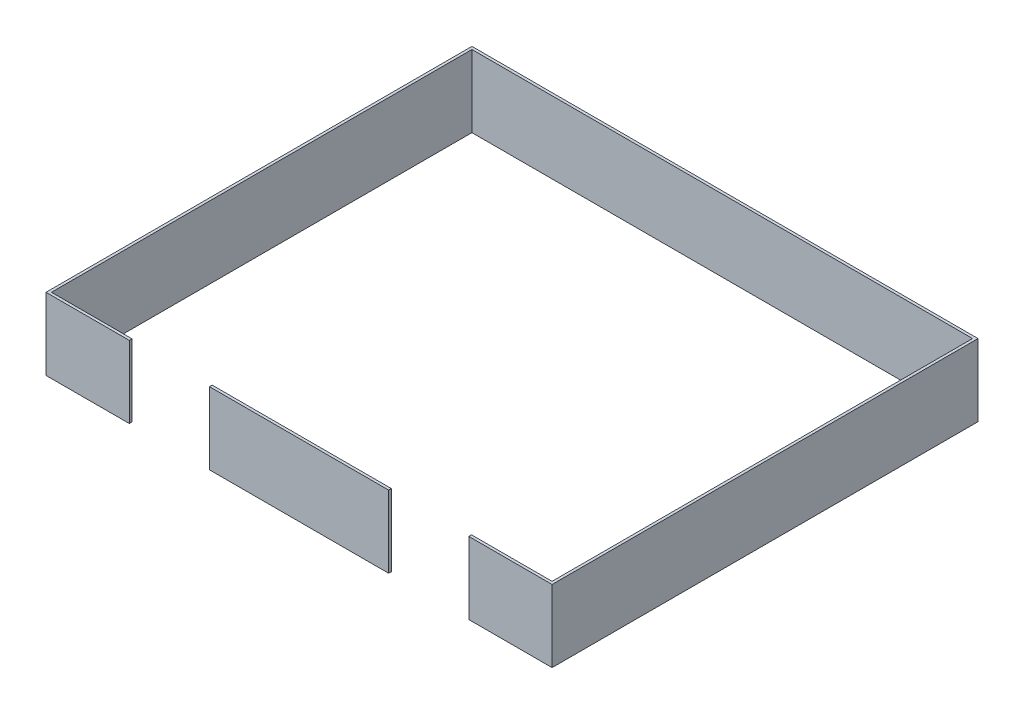
SolidWorks part; units mm, degrees
ref_plane "Front Plane" through (0, 0, 0) normal (0, 0, 1) x (1, 0, 0)
ref_plane "Top Plane" through (0, 0, 0) normal (0, 1, 0) x (1, 0, 0)
ref_plane "Right Plane" through (0, 0, 0) normal (1, 0, 0) x (0, 0, -1)
sketch "Sketch1" plane through (0, 0, 0) normal (0, 1, 0) x (1, 0, 0)
  line L1 (3568.7, 3003.55) -> (-3568.7, 3003.55)
  line L2 (3568.7, 3003.55) -> (3568.7, -3003.55)
  line L3 (3568.7, -3003.55) -> (-3568.7, -3003.55)
  line L4 (-3568.7, 3003.55) -> (-3568.7, -3003.55)
  line L5 (3568.7, 3003.55) -> (-3568.7, -3003.55) construction
  line L6 (3568.7, -3003.55) -> (-3568.7, 3003.55) construction
  line L7 (-3530.6, 2965.45) -> (3530.6, 2965.45)
  line L8 (-3530.6, 2965.45) -> (-3530.6, -2965.45)
  line L9 (-3530.6, -2965.45) -> (3530.6, -2965.45)
  line L10 (3530.6, 2965.45) -> (3530.6, -2965.45)
  line L11 (-3530.6, 2965.45) -> (3530.6, -2965.45) construction
  line L12 (-3530.6, -2965.45) -> (3530.6, 2965.45) construction
  point P0 (0, 0)
  point P5 (0, 0)
  dimension "D1" = 38.1
  dimension "D2" = 6007.1
  dimension "D3" = 7137.4
  dimension "D4" = 38.1
extrude "Boss-Extrude1" add sketch "Sketch1" along normal blind 1016 contours L2 L1 L4 L3 | L8 L7 L10 L9
sketch "Sketch2" plane through (0, 1016, 0) normal (0, 1, 0) x (1, 0, 0)
  line L0 (-2393.95, -2965.45) -> (-2393.95, -3003.55)
  line L1 (-3530.6, -2965.45) -> (3530.6, -2965.45) construction
  line L2 (3568.7, -3003.55) -> (-3568.7, -3003.55) construction
  line L3 (-2393.95, -3003.55) -> (-1263.65, -3003.55)
  line L4 (-1263.65, -3003.55) -> (-1263.65, -2965.45)
  line L5 (-1263.65, -2965.45) -> (-2393.95, -2965.45)
  line L6 (1263.65, -2965.45) -> (1263.65, -3003.55)
  line L7 (1263.65, -3003.55) -> (2393.95, -3003.55)
  line L8 (2393.95, -3003.55) -> (2393.95, -2965.45)
  line L9 (2393.95, -2965.45) -> (1263.65, -2965.45)
  line L10 (-3568.7, 3003.55) -> (-3568.7, -3003.55) construction
  line L11 (3568.7, 3003.55) -> (3568.7, -3003.55) construction
  dimension "D1" = 1174.75
  dimension "D2" = 1174.75
  dimension "D3" = 1130.3
extrude "Cut-Extrude1" cut sketch "Sketch2" against normal blind 2048.764
